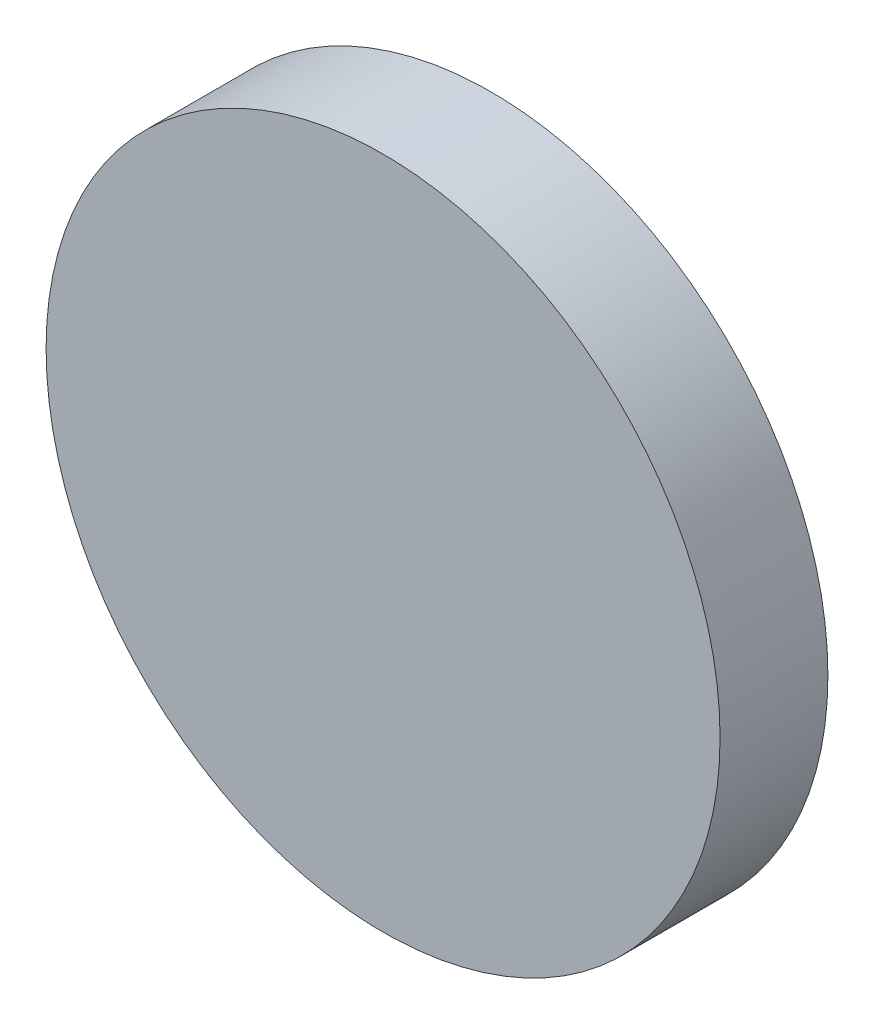
SolidWorks part; units mm, degrees
ref_plane "前视基准面" through (0, 0, 0) normal (0, 0, 1) x (1, 0, 0)
ref_plane "上视基准面" through (0, 0, 0) normal (0, 1, 0) x (1, 0, 0)
ref_plane "右视基准面" through (0, 0, 0) normal (1, 0, 0) x (0, 0, -1)
sketch "草图1" plane through (0, 0, 0) normal (0, 0, 1) x (1, 0, 0)
  circle A0 centre (0, 0) radius 12.5
  dimension "D1" = 25
extrude "凸台-拉伸1" add sketch "草图1" along normal blind 4 contours A0
